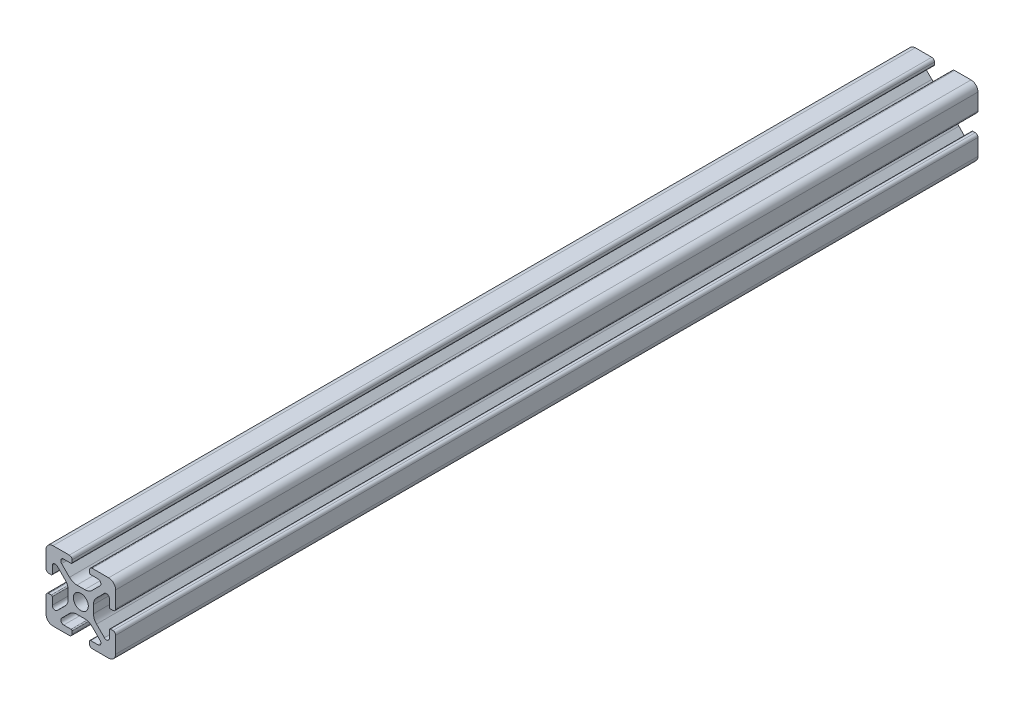
SolidWorks part; units mm, degrees
material "6061-T6 (SS)"
ref_plane "Front Plane" through (0, 0, 0) normal (0, 0, 1) x (1, 0, 0)
ref_plane "Top Plane" through (0, 0, 0) normal (0, 1, 0) x (1, 0, 0)
ref_plane "Right Plane" through (0, 0, 0) normal (1, 0, 0) x (0, 0, -1)
sketch "Sketch1" plane through (0, 0, 0) normal (0, 0, 1) x (1, 0, 0)
  line L2 (-9.9949, 7.9883) -> (-9.9949, 3.2893)
  line L3 (-7.9883, 9.9949) -> (-3.2893, 9.9949)
  line L4 (-2.5019, 9.2075) -> (-2.5019, 8.4963)
  line L5 (-2.8067, 8.1915) -> (-4.9149, 8.1915)
  line L6 (-5.5076, 6.7606) -> (-3.2528, 4.5058)
  line L7 (-6.7606, 5.5076) -> (-4.5058, 3.2528)
  line L8 (-8.1915, 4.9149) -> (-8.1915, 2.8067)
  line L9 (-8.4963, 2.5019) -> (-9.2075, 2.5019)
  line L11 (-1.1334, 3.6279) -> (1.1334, 3.6279)
  line L12 (-3.6279, 1.1334) -> (-3.6279, -1.1334)
  line L13 (8.4963, 2.5019) -> (9.2075, 2.5019)
  line L14 (8.1915, 4.9149) -> (8.1915, 2.8067)
  line L15 (9.9949, 7.9883) -> (9.9949, 3.2893)
  line L16 (7.9883, 9.9949) -> (3.2893, 9.9949)
  line L17 (2.5019, 9.2075) -> (2.5019, 8.4963)
  line L18 (2.8067, 8.1915) -> (4.9149, 8.1915)
  line L19 (3.6279, 1.1334) -> (3.6279, -1.1334)
  line L20 (5.5076, 6.7606) -> (3.2528, 4.5058)
  line L21 (6.7606, 5.5076) -> (4.5058, 3.2528)
  line L22 (-8.4963, -2.5019) -> (-9.2075, -2.5019)
  line L23 (-8.1915, -4.9149) -> (-8.1915, -2.8067)
  line L24 (-6.7606, -5.5076) -> (-4.5058, -3.2528)
  line L25 (-5.5076, -6.7606) -> (-3.2528, -4.5058)
  line L26 (-2.8067, -8.1915) -> (-4.9149, -8.1915)
  line L27 (-2.5019, -9.2075) -> (-2.5019, -8.4963)
  line L28 (-7.9883, -9.9949) -> (-3.2893, -9.9949)
  line L29 (-9.9949, -7.9883) -> (-9.9949, -3.2893)
  line L30 (9.9949, -7.9883) -> (9.9949, -3.2893)
  line L31 (7.9883, -9.9949) -> (3.2893, -9.9949)
  line L32 (2.5019, -9.2075) -> (2.5019, -8.4963)
  line L33 (2.8067, -8.1915) -> (4.9149, -8.1915)
  line L34 (5.5076, -6.7606) -> (3.2528, -4.5058)
  line L35 (6.7606, -5.5076) -> (4.5058, -3.2528)
  line L36 (8.1915, -4.9149) -> (8.1915, -2.8067)
  line L37 (8.4963, -2.5019) -> (9.2075, -2.5019)
  line L38 (-1.1334, -3.6279) -> (1.1334, -3.6279)
  circle A0 centre (0, 0) radius 2.1463
  arc A1 (-9.9949, 7.9883) -> (-7.9883, 9.9949) centre (-7.9883, 7.9883) cw
  arc A2 (-6.7606, 5.5076) -> (-8.1915, 4.9149) centre (-7.3533, 4.9149) ccw
  arc A3 (-4.9149, 8.1915) -> (-5.5076, 6.7606) centre (-4.9149, 7.3533) ccw
  arc A4 (-3.2893, 9.9949) -> (-2.5019, 9.2075) centre (-3.2893, 9.2075) cw
  arc A5 (-9.9949, 3.2893) -> (-9.2075, 2.5019) centre (-9.2075, 3.2893) ccw
  arc A6 (-8.1915, 2.8067) -> (-8.4963, 2.5019) centre (-8.4963, 2.8067) cw
  arc A7 (-2.5019, 8.4963) -> (-2.8067, 8.1915) centre (-2.8067, 8.4963) cw
  arc A8 (-1.1334, 3.6279) -> (-3.2528, 4.5058) centre (-1.1334, 6.6251) cw
  arc A9 (-3.6279, 1.1334) -> (-4.5058, 3.2528) centre (-6.6251, 1.1334) ccw
  arc A10 (8.1915, 2.8067) -> (8.4963, 2.5019) centre (8.4963, 2.8067) ccw
  arc A11 (9.9949, 3.2893) -> (9.2075, 2.5019) centre (9.2075, 3.2893) cw
  arc A12 (9.9949, 7.9883) -> (7.9883, 9.9949) centre (7.9883, 7.9883) ccw
  arc A13 (3.2893, 9.9949) -> (2.5019, 9.2075) centre (3.2893, 9.2075) ccw
  arc A14 (2.5019, 8.4963) -> (2.8067, 8.1915) centre (2.8067, 8.4963) ccw
  arc A15 (1.1334, 3.6279) -> (3.2528, 4.5058) centre (1.1334, 6.6251) ccw
  arc A16 (3.6279, 1.1334) -> (4.5058, 3.2528) centre (6.6251, 1.1334) cw
  arc A17 (6.7606, 5.5076) -> (8.1915, 4.9149) centre (7.3533, 4.9149) cw
  arc A18 (4.9149, 8.1915) -> (5.5076, 6.7606) centre (4.9149, 7.3533) cw
  arc A19 (-3.6279, -1.1334) -> (-4.5058, -3.2528) centre (-6.6251, -1.1334) cw
  arc A20 (-1.1334, -3.6279) -> (-3.2528, -4.5058) centre (-1.1334, -6.6251) ccw
  arc A21 (-2.5019, -8.4963) -> (-2.8067, -8.1915) centre (-2.8067, -8.4963) ccw
  arc A22 (-8.1915, -2.8067) -> (-8.4963, -2.5019) centre (-8.4963, -2.8067) ccw
  arc A23 (-9.9949, -3.2893) -> (-9.2075, -2.5019) centre (-9.2075, -3.2893) cw
  arc A24 (-3.2893, -9.9949) -> (-2.5019, -9.2075) centre (-3.2893, -9.2075) ccw
  arc A25 (-4.9149, -8.1915) -> (-5.5076, -6.7606) centre (-4.9149, -7.3533) cw
  arc A26 (-6.7606, -5.5076) -> (-8.1915, -4.9149) centre (-7.3533, -4.9149) cw
  arc A27 (-9.9949, -7.9883) -> (-7.9883, -9.9949) centre (-7.9883, -7.9883) ccw
  arc A28 (9.9949, -7.9883) -> (7.9883, -9.9949) centre (7.9883, -7.9883) cw
  arc A29 (6.7606, -5.5076) -> (8.1915, -4.9149) centre (7.3533, -4.9149) ccw
  arc A30 (4.9149, -8.1915) -> (5.5076, -6.7606) centre (4.9149, -7.3533) ccw
  arc A31 (3.2893, -9.9949) -> (2.5019, -9.2075) centre (3.2893, -9.2075) cw
  arc A32 (9.9949, -3.2893) -> (9.2075, -2.5019) centre (9.2075, -3.2893) ccw
  arc A33 (8.1915, -2.8067) -> (8.4963, -2.5019) centre (8.4963, -2.8067) cw
  arc A34 (2.5019, -8.4963) -> (2.8067, -8.1915) centre (2.8067, -8.4963) cw
  arc A35 (1.1334, -3.6279) -> (3.2528, -4.5058) centre (1.1334, -6.6251) cw
  arc A36 (3.6279, -1.1334) -> (4.5058, -3.2528) centre (6.6251, -1.1334) ccw
extrude "Boss-Extrude1" add sketch "Sketch1" along normal mid plane 375
sketch "Sketch2" plane through (0, 9.9949, 0) normal (0, 1, 0) x (1, 0, 0)
  line L1 (-25.2826, 60) -> (36.2443, 60)
  line L2 (-25.2826, 60) -> (-25.2826, 212.7566)
  line L3 (-25.2826, 212.7566) -> (36.2443, 212.7566)
  line L4 (36.2443, 60) -> (36.2443, 212.7566)
  dimension "D1" = 60
extrude "Cut-Extrude1" cut sketch "Sketch2" against normal through all
